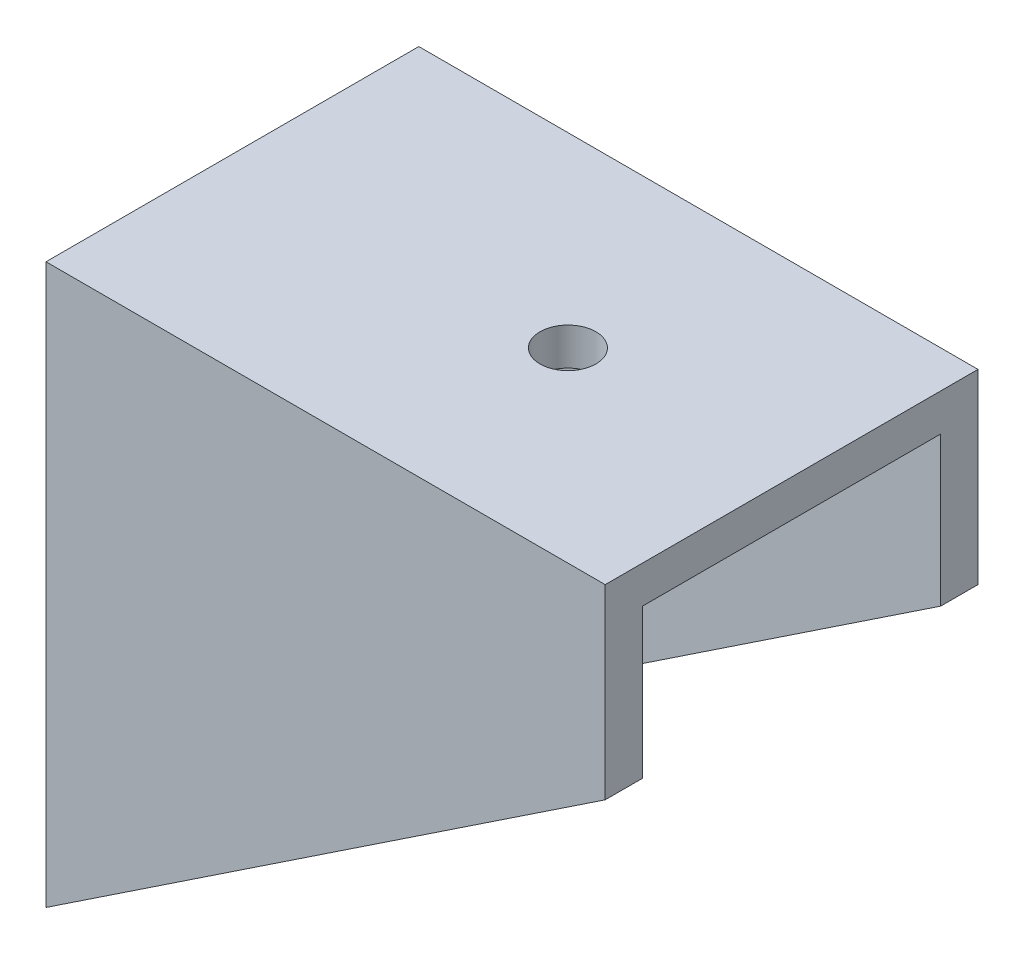
SolidWorks part; units mm, degrees
ref_plane "Спереди" through (0, 0, 0) normal (0, 0, 1) x (1, 0, 0)
ref_plane "Сверху" through (0, 0, 0) normal (0, 1, 0) x (1, 0, 0)
ref_plane "Справа" through (0, 0, 0) normal (1, 0, 0) x (0, 0, -1)
sketch "Эскиз1" plane through (0, 0, 0) normal (1, 0, 0) x (0, 0, -1)
  line L0 (0, 0) -> (0, 30)
  line L1 (0, 30) -> (20, 30)
  line L2 (20, 30) -> (20, 0)
extrude "Вытянуть-Тонкостенный1" add sketch "Эскиз1" along normal blind 30 thin
sketch "Эскиз2" plane through (0, 0, 0) normal (0, 0, 1) x (1, 0, 0)
  line L0 (0, 0) -> (30, 20)
  line L1 (30, 0) -> (30, 30) construction
  line L2 (30, 20) -> (30, 0)
  line L3 (30, 0) -> (0, 0)
extrude "Вырез-Вытянуть1" cut sketch "Эскиз2" against normal through all
sketch "Эскиз3" plane through (0, 30, 0) normal (0, 1, 0) x (1, 0, 0)
  circle A0 centre (18, 10) radius 1.5
extrude "Вырез-Вытянуть2" cut sketch "Эскиз3" against normal through all
